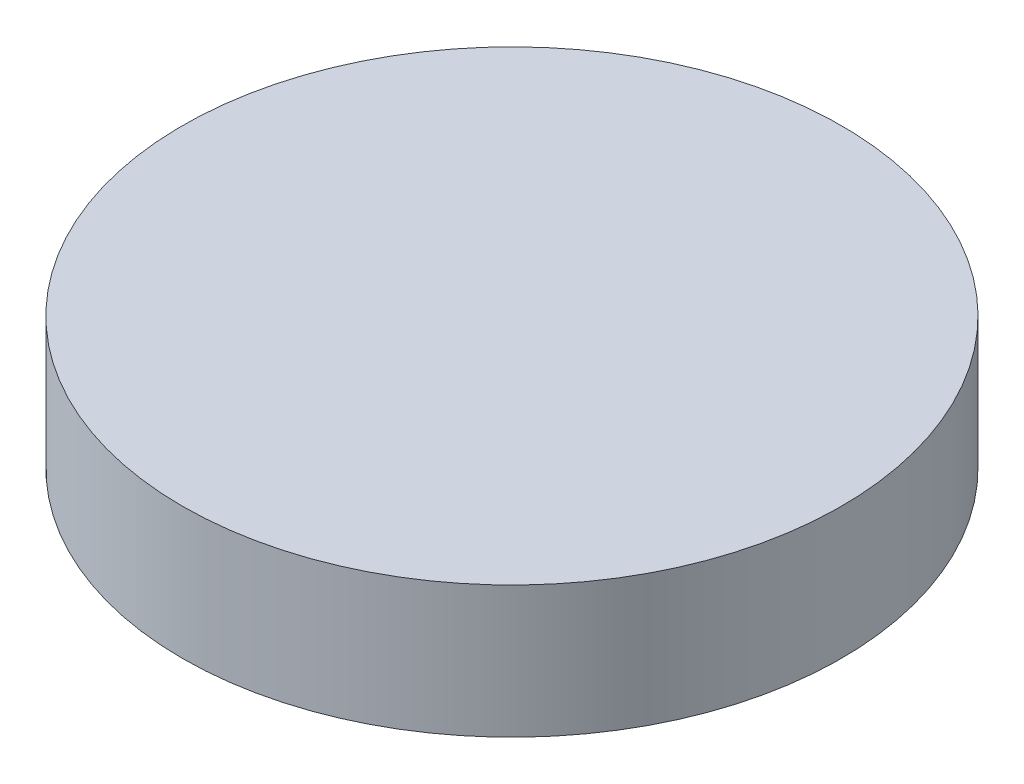
SolidWorks part; units mm, degrees
ref_plane "Front" through (0, 0, 0) normal (0, 0, 1) x (1, 0, 0)
ref_plane "Top" through (0, 0, 0) normal (0, 1, 0) x (1, 0, 0)
ref_plane "Right" through (0, 0, 0) normal (1, 0, 0) x (0, 0, -1)
sketch "Sketch1" plane through (0, 0, 0) normal (0, 1, 0) x (1, 0, 0)
  circle A0 centre (0, 0) radius 6.35
  dimension "D1" = 12.7
extrude "Extrude1" add sketch "Sketch1" along normal blind 2.54
